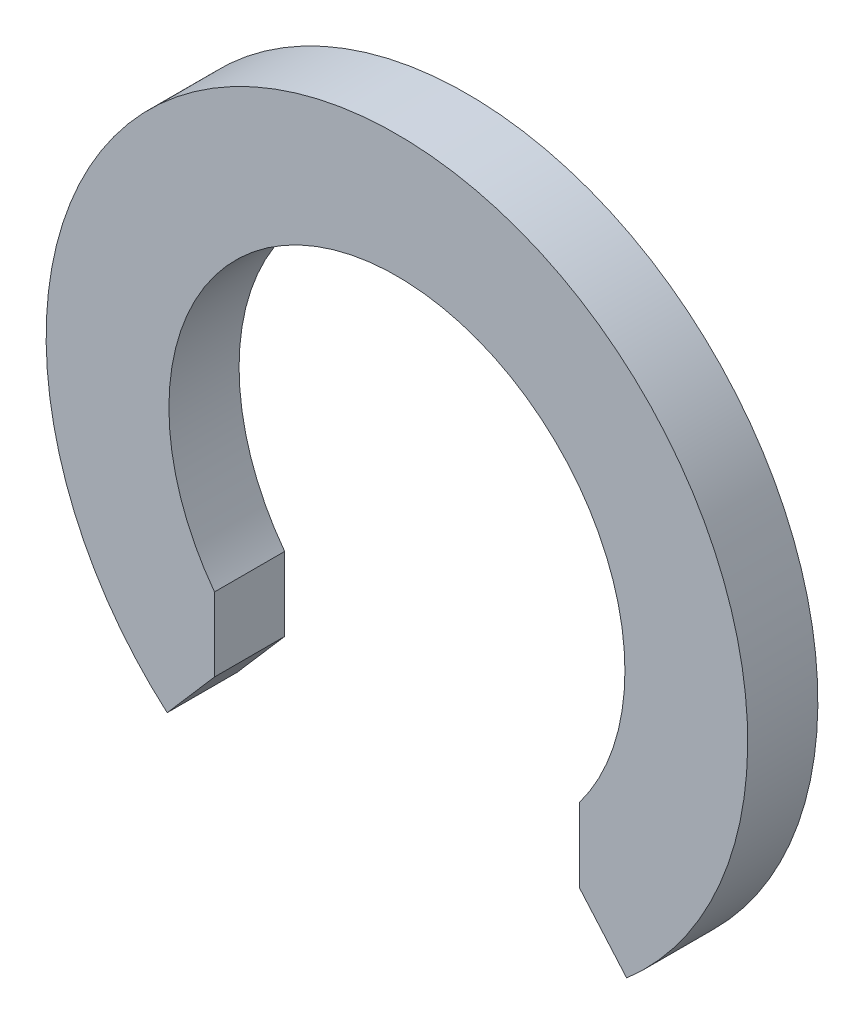
SolidWorks part; units mm, degrees
ref_plane "Alzado" through (0, 0, 0) normal (0, 0, 1) x (1, 0, 0)
ref_plane "Planta" through (0, 0, 0) normal (0, 1, 0) x (1, 0, 0)
ref_plane "Vista lateral" through (0, 0, 0) normal (1, 0, 0) x (0, 0, -1)
sketch "Croquis1" plane through (0, 0, 0) normal (0, 0, 1) x (1, 0, 0)
  circle A0 centre (0, 0) radius 3.25
  circle A1 centre (0, 0) radius 5
  dimension "D1" = 6.5
  dimension "D2" = 10
extrude "Saliente-Extruir1" add sketch "Croquis1" along normal blind 1
sketch "Croquis2" plane through (0, 0, 1) normal (0, 0, 1) x (1, 0, 0)
  line L0 (-2.6, -3) -> (-3.2747, -3.7784)
  line L1 (2.6, 0) -> (-2.6, 0)
  line L2 (2.6, 0) -> (2.6, -3)
  line L3 (2.6, -6) -> (-2.6, -6)
  line L4 (-2.6, 0) -> (-2.6, -3)
  line L5 (2.6, -3) -> (3.2747, -3.7784)
  line L6 (-3.2747, -3.7784) -> (-3.2747, -6)
  line L7 (-3.2747, -6) -> (-2.6, -6)
  line L8 (2.6, -6) -> (3.2747, -6)
  line L9 (3.2747, -6) -> (3.2747, -3.7784)
  circle A1 centre (0, 0) radius 5 construction
  dimension "D1" = 2.6
  dimension "D2" = 2.6
  dimension "D3" = 6
extrude "Cortar-Extruir1" cut sketch "Croquis2" against normal blind 10
